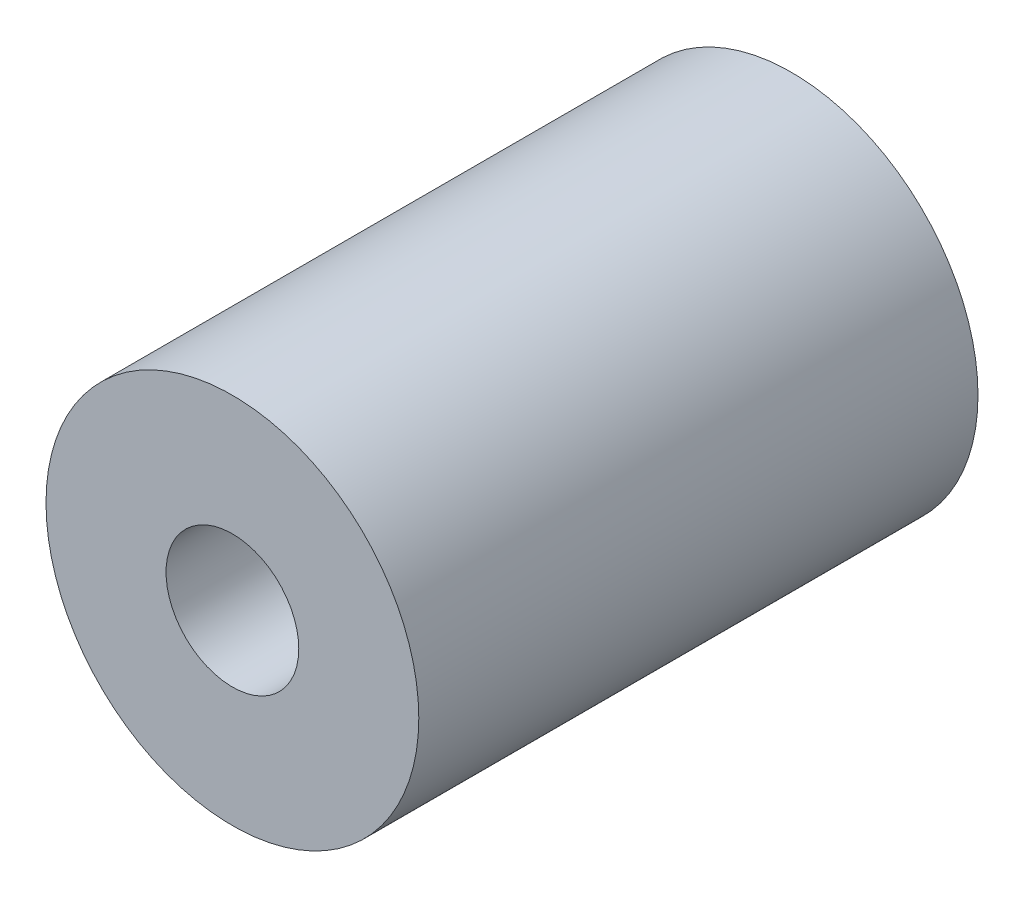
SolidWorks part; units mm, degrees
ref_plane "Front" through (0, 0, 0) normal (0, 0, 1) x (1, 0, 0)
ref_plane "Top" through (0, 0, 0) normal (0, 1, 0) x (1, 0, 0)
ref_plane "Right" through (0, 0, 0) normal (1, 0, 0) x (0, 0, -1)
sketch "face" plane through (0, 0, 0) normal (0, 0, 1) x (1, 0, 0)
  circle A0 centre (0, 0) radius 3.175
  circle A1 centre (0, 0) radius 1.1303
  dimension "OD" = 6.35
  dimension "ID" = 2.2606
extrude "washer" add sketch "face" against normal blind 9.525
